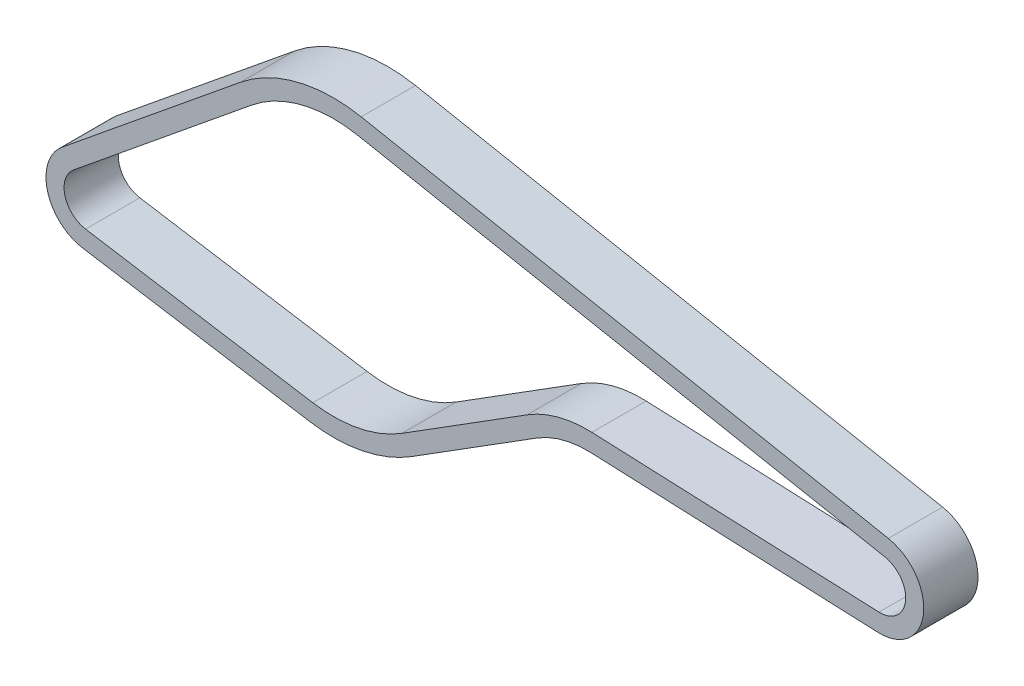
SolidWorks part; units mm, degrees
material "NEOPRENE"
ref_plane "Plano frontal" through (0, 0, 0) normal (0, 0, 1) x (1, 0, 0)
ref_plane "Plano superior" through (0, 0, 0) normal (0, 1, 0) x (1, 0, 0)
ref_plane "Plano direito" through (0, 0, 0) normal (1, 0, 0) x (0, 0, -1)
sketch "Esboço1" plane through (0, 0, 0) normal (0, 0, 1) x (1, 0, 0)
  line L0 (4.3312, 22.4867) -> (91.7635, 5.6462) construction
  line L1 (42.0897, -2.2155) -> (42.0897, -5.2155) construction
  line L2 (4.0475, 21.0138) -> (91.4798, 4.1733)
  line L3 (-41.1086, -15.0286) -> (-3.4171, -21.1254)
  line L4 (4.6149, 23.9596) -> (92.0472, 7.1191)
  line L5 (-41.5876, -17.9901) -> (-3.8962, -24.0869)
  line L6 (0, 0) -> (-27.7334, 0) construction
  line L7 (0, 0) -> (-40.4299, -10.8332) construction
  line L8 (12.9793, -20.6615) -> (33.7383, -7.621)
  line L9 (-45.011, -5.2139) -> (-15.4177, 18.9118)
  line L10 (-40.4299, -3.5832) -> (-40.4299, -6.5832) construction
  line L11 (-43.1154, -7.5391) -> (-13.522, 16.5866)
  line L12 (42.7531, -5.2295) -> (90.3696, -7.2435)
  line L13 (11.3835, -18.1212) -> (32.1424, -5.0807)
  line L14 (42.8799, -2.2322) -> (90.4964, -4.2462)
  circle A6 centre (0, 0) radius 22.9 construction
  circle A7 centre (90.676, 0) radius 5.75 construction
  circle A8 centre (0, 0) radius 24.4
  circle A9 centre (90.676, 0) radius 7.25
  circle A10 centre (0, 0) radius 21.4
  circle A11 centre (90.676, 0) radius 4.25
  circle A12 centre (-40.4299, -10.8332) radius 5.75 construction
  circle A13 centre (-40.4299, -10.8332) radius 7.25
  circle A14 centre (-40.4299, -10.8332) radius 4.25
  circle A15 centre (42.0897, -20.9155) radius 17.2 construction
  circle A16 centre (42.0897, -20.9155) radius 15.7
  circle A17 centre (42.0897, -20.9155) radius 18.7
  point P21 (42.0897, -5.2155)
  point P22 (42.0897, -2.2155)
  point P29 (-40.4299, -3.5832)
  point P30 (-40.4299, -6.5832)
  point P38 (-40.4299, -5.0832)
  point P41 (42.0897, -3.7155)
  dimension "D5" = 1.5
  dimension "D3" = 11.5
  dimension "D12" = 34.4
  dimension "D13" = 45.8
  dimension "D2" = 90.676
  dimension "D6" = 15
  dimension "D7" = 41.8561
  dimension "D8" = 3
  dimension "D9" = 47
  dimension "D10" = 52.897
  dimension "D11" = 3
  dimension "D4" = 1.5
extrude "Ressalto-extrusão1" add sketch "Esboço1" along normal mid plane 9
